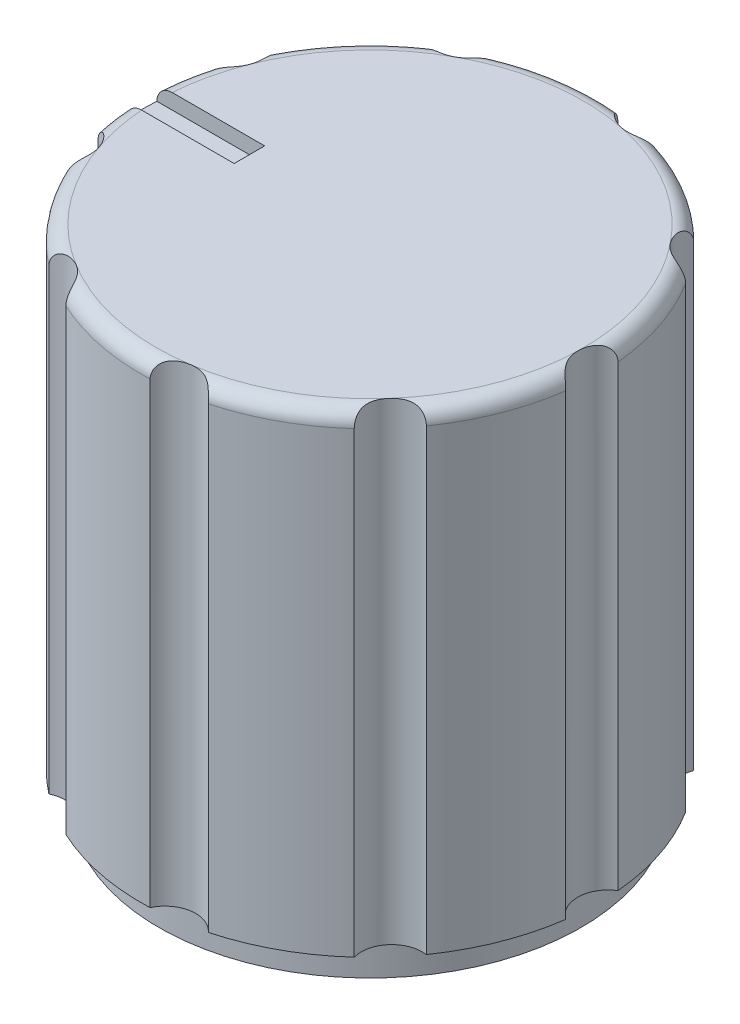
SolidWorks part; units mm, degrees
material "Custom Plastic"
ref_plane "Front Plane" through (0, 0, 0) normal (0, 0, 1) x (1, 0, 0)
ref_plane "Top Plane" through (0, 0, 0) normal (0, 1, 0) x (1, 0, 0)
ref_plane "Right Plane" through (0, 0, 0) normal (1, 0, 0) x (0, 0, -1)
sketch "Sketch1" plane through (0, 0, 0) normal (0, 1, 0) x (1, 0, 0)
  circle A0 centre (0, 0) radius 7.5
  dimension "D1" = 15
extrude "Boss-Extrude1" add sketch "Sketch1" along normal blind 16.5
fillet "Fillet1" radius 0.5 1 edges at (0, 16.5, 7.5)
sketch "Sketch2" plane through (0, 0, 0) normal (0, -1, 0) x (1, 0, 0)
  circle A0 centre (0, 0) radius 2.7504
extrude "Cut-Extrude1" cut sketch "Sketch2" against normal blind 5 contours A0
sketch "Sketch3" plane through (0, 0, 0) normal (0, -1, 0) x (1, 0, 0)
  circle A0 centre (0, 0) radius 6.915
  circle A1 centre (0, 0) radius 7.5
extrude "Cut-Extrude2" cut sketch "Sketch3" against normal blind 1
sketch "Sketch4" plane through (0, 16.5, 0) normal (0, 1, 0) x (1, 0, 0)
  circle A0 centre (1.1989, -7.9097) radius 1
  circle A1 centre (0, 0) radius 7 construction
  circle A2 centre (-4.1658, -6.8298) radius 1
  circle A3 centre (-7.5813, -2.5542) radius 1
  circle A4 centre (-7.4494, 2.9165) radius 1
  circle A5 centre (-3.8319, 7.0226) radius 1
  circle A6 centre (1.5786, 7.8427) radius 1
  circle A7 centre (6.2505, 4.9931) radius 1
  circle A8 centre (7.9977, -0.1928) radius 1
  circle A9 centre (6.0027, -5.2885) radius 1
  dimension "D1" = 2
  dimension "D2" = 14
  dimension "D3" = 9
extrude "Cut-Extrude3" cut sketch "Sketch4" against normal through all
sketch "Sketch5" plane through (0, 16.5, 0) normal (0, 1, 0) x (1, 0, 0)
  line L0 (-3.9516, 0) -> (-10.7367, 0) construction
  line L1 (-7.9512, 0.5) -> (-3.9516, 0.5)
  line L2 (-7.9512, 0.5) -> (-7.9512, -0.5)
  line L3 (-7.9512, -0.5) -> (-3.9516, -0.5)
  line L4 (-3.9516, 0.5) -> (-3.9516, -0.5)
  dimension "D1" = 1
extrude "Cut-Extrude4" cut sketch "Sketch5" against normal blind 0.5
